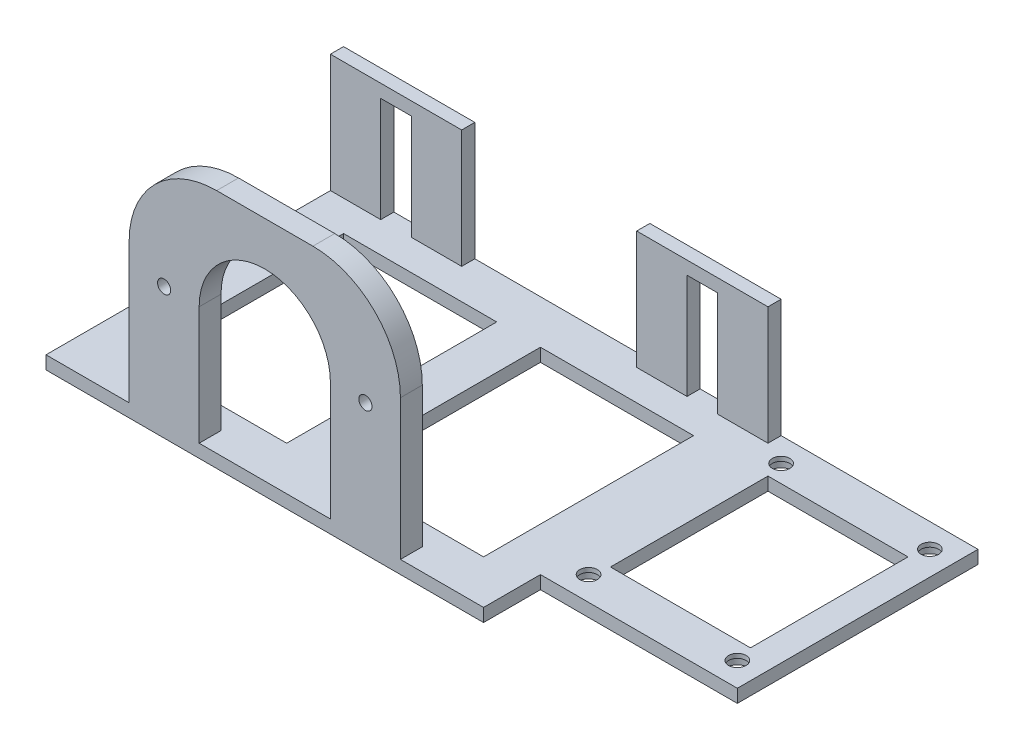
SolidWorks part; units mm, degrees
ref_plane "정면" through (0, 0, 0) normal (0, 0, 1) x (1, 0, 0)
ref_plane "윗면" through (0, 0, 0) normal (0, 1, 0) x (1, 0, 0)
ref_plane "우측면" through (0, 0, 0) normal (1, 0, 0) x (0, 0, -1)
sketch "스케치1" plane through (0, 0, 0) normal (0, 1, 0) x (1, 0, 0)
  line L1 (-50, 34) -> (50, 34)
  line L2 (-50, 34) -> (-50, -34)
  line L3 (-50, -34) -> (50, -34)
  line L4 (50, 34) -> (50, -34)
  line L5 (-50, 34) -> (50, -34) construction
  line L6 (-50, -34) -> (50, 34) construction
  point P0 (0, 0)
  dimension "D1" = 100
  dimension "D2" = 68
extrude "보스-돌출1" add sketch "스케치1" along normal blind 3
sketch "스케치2" plane through (0, 3, 0) normal (0, 1, 0) x (1, 0, 0)
  line L0 (-50, 34) -> (-50, -34) construction
  line L1 (50, 34) -> (-50, 34)
  line L2 (50, 34) -> (50, 31)
  line L3 (50, 31) -> (-50, 31)
  line L4 (-50, 34) -> (-50, 31)
  dimension "D1" = 3
extrude "보스-돌출2" add sketch "스케치2" along normal blind 27
sketch "스케치3" plane through (0, 0, -31) normal (0, 0, 1) x (1, 0, 0)
  line L0 (-50, 3) -> (50, 3) construction
  line L1 (-38.5, 27) -> (-31.5, 27)
  line L2 (-38.5, 27) -> (-38.5, 3)
  line L3 (-38.5, 3) -> (-31.5, 3)
  line L4 (-31.5, 27) -> (-31.5, 3)
  line L5 (-50, 30) -> (-50, 3) construction
  line L6 (-50, 3) -> (50, 3) construction
  line L7 (31.5, 27) -> (38.5, 27)
  line L8 (31.5, 27) -> (31.5, 3)
  line L9 (31.5, 3) -> (38.5, 3)
  line L10 (38.5, 27) -> (38.5, 3)
  line L11 (50, 30) -> (50, 3) construction
  dimension "D1" = 24
  dimension "D2" = 11.5
  dimension "D3" = 7
  dimension "D4" = 7
  dimension "D5" = 24
  dimension "D6" = 11.5
extrude "컷-돌출2" cut sketch "스케치3" against normal blind 27
sketch "스케치4" plane through (0, 3, 0) normal (0, 1, 0) x (1, 0, 0)
  line L0 (-50, -34) -> (50, -34) construction
  line L1 (-31, -29) -> (31, -29)
  line L2 (-31, -29) -> (-31, -34)
  line L3 (-31, -34) -> (31, -34)
  line L4 (31, -29) -> (31, -34)
  line L5 (50, -34) -> (50, 31) construction
  dimension "D1" = 5
  dimension "D2" = 62
  dimension "D3" = 19
extrude "보스-돌출3" add sketch "스케치4" along normal blind 52 contours L1 L4 L3 L2
sketch "스케치5" plane through (0, 0, 34) normal (0, 0, 1) x (1, 0, 0)
  line L0 (0, 55) -> (0, 0) construction
  line L1 (-50, 0) -> (50, 0) construction
  line L2 (-31, 55) -> (31, 55) construction
  line L3 (-15, 30) -> (-15, 3)
  line L4 (-15, 55) -> (15, 55)
  line L5 (-15, 3) -> (15, 3)
  line L6 (15, 3) -> (15, 30)
  arc A0 (15, 30) -> (-15, 30) centre (0, 30) ccw
  circle A1 centre (-23, 30) radius 1.5
  circle A2 centre (23, 30) radius 1.5
  point P4 (0, 30)
  dimension "D2" = 15
  dimension "D4" = 3
  dimension "D7" = 23
  dimension "D1" = 30
  dimension "D3" = 3
  dimension "D5" = 23
  dimension "D6" = 30
extrude "컷-돌출4" cut sketch "스케치5" against normal blind 5
sketch "스케치7" plane through (0, 0, 0) normal (0, -1, 0) x (1, 0, 0)
  line L0 (50, 34) -> (50, -34) construction
  line L1 (40, 24) -> (5, 24)
  line L2 (40, 24) -> (40, -24)
  line L3 (40, -24) -> (5, -24)
  line L4 (5, 24) -> (5, -24)
  line L5 (50, -34) -> (-50, -34) construction
  line L6 (-50, 34) -> (50, 34) construction
  line L7 (-50, -34) -> (-50, 34) construction
  line L8 (-5, 24) -> (-40, 24)
  line L9 (-5, 24) -> (-5, -24)
  line L10 (-5, -24) -> (-40, -24)
  line L11 (-40, 24) -> (-40, -24)
  dimension "D1" = 10
  dimension "D2" = 10
  dimension "D3" = 10
  dimension "D4" = 10
  dimension "D5" = 10
  dimension "D6" = 10
  dimension "D7" = 5
  dimension "D8" = 5
extrude "컷-돌출5" cut sketch "스케치7" against normal blind 3
sketch "스케치8" plane through (50, 0, 0) normal (1, 0, 0) x (0, 0, -1)
  line L0 (-34, 3) -> (31, 3) construction
  line L1 (34, 0) -> (-21, 0)
  line L2 (34, 0) -> (34, 3)
  line L3 (34, 3) -> (-21, 3)
  line L4 (-21, 0) -> (-21, 3)
  dimension "D1" = 55
extrude "보스-돌출4" add sketch "스케치8" along normal blind 45
sketch "스케치10" plane through (0, 3, 0) normal (0, 1, 0) x (1, 0, 0)
  line L0 (95, -21) -> (50, -21) construction
  line L1 (52.5, -18.5) -> (92.5, -18.5) construction
  line L2 (52.5, -18.5) -> (52.5, 31.5) construction
  line L3 (52.5, 31.5) -> (92.5, 31.5) construction
  line L4 (92.5, -18.5) -> (92.5, 31.5) construction
  line L5 (95, 34) -> (95, -21) construction
  line L6 (52.5, 6.5) -> (92.5, 6.5) construction
  line L7 (72.5, -18.5) -> (72.5, 31.5) construction
  line L8 (0, -34) -> (0, 34) construction
  line L9 (50, 34) -> (-50, 34) construction
  line L11 (56.5, 24.5) -> (88.5, 24.5)
  line L12 (56.5, 24.5) -> (56.5, -11.5)
  line L13 (56.5, -11.5) -> (88.5, -11.5)
  line L14 (88.5, 24.5) -> (88.5, -11.5)
  circle A0 centre (55.5, -15.5) radius 2
  circle A1 centre (55.5, 28.5) radius 2
  circle A2 centre (89.5, 28.5) radius 2
  circle A3 centre (89.5, -15.5) radius 2
  dimension "D1" = 4
  dimension "D2" = 4
  dimension "D3" = 4
  dimension "D4" = 7
  dimension "D10" = 3
  dimension "D11" = 7
  dimension "D5" = 50
  dimension "D6" = 40
  dimension "D7" = 2.5
  dimension "D8" = 2.5
  dimension "D9" = 3
extrude "컷-돌출6" cut sketch "스케치10" against normal blind 45
sketch "스케치12" plane through (0, 0, 0) normal (0, -1, 0) x (1, 0, 0)
  line L1 (89.5, -28.5) -> (55.5, -28.5) construction
  line L2 (89.5, -28.5) -> (89.5, 15.5) construction
  line L3 (89.5, 15.5) -> (55.5, 15.5) construction
  line L4 (55.5, -28.5) -> (55.5, 15.5) construction
  circle A0 centre (89.5, -28.5) radius 3
  circle A1 centre (89.5, 15.5) radius 3
  circle A2 centre (55.5, 15.5) radius 3
  circle A3 centre (55.5, -28.5) radius 3
  dimension "D1" = 6
  dimension "D2" = 6
  dimension "D3" = 6
  dimension "D4" = 6
extrude "컷-돌출7" cut sketch "스케치12" against normal blind 2
sketch "스케치13" plane through (0, 0, -34) normal (0, 0, -1) x (-1, 0, 0)
  line L0 (-50, 30) -> (50, 30) construction
  line L1 (-20, 30) -> (20, 30)
  line L2 (-20, 30) -> (-20, 3)
  line L3 (-20, 3) -> (20, 3)
  line L4 (20, 30) -> (20, 3)
  line L5 (-95, 0) -> (50, 0) construction
  line L6 (-31.5, 27) -> (-31.5, 3) construction
  line L7 (31.5, 3) -> (31.5, 27) construction
  dimension "D1" = 3
  dimension "D2" = 11.5
  dimension "D3" = 11.5
extrude "컷-돌출8" cut sketch "스케치13" against normal blind 10
fillet "필렛1" radius 20 2 edges at (-31, 55, 31.5) (31, 55, 31.5)
